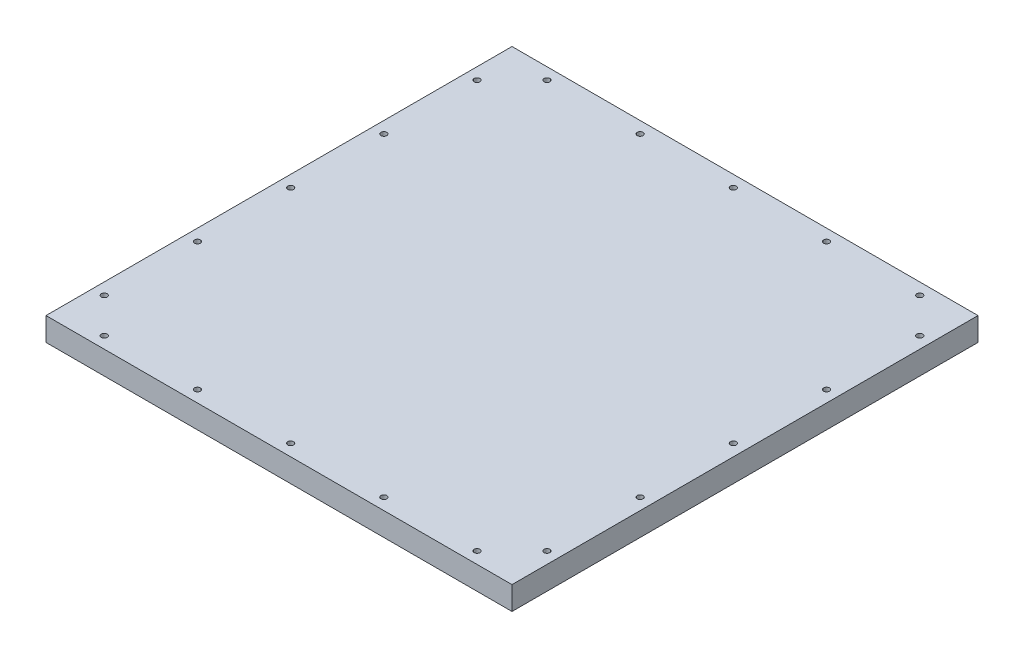
SolidWorks part; units mm, degrees
ref_plane "Front Plane" through (0, 0, 0) normal (0, 0, 1) x (1, 0, 0)
ref_plane "Top Plane" through (0, 0, 0) normal (0, 1, 0) x (1, 0, 0)
ref_plane "Right Plane" through (0, 0, 0) normal (1, 0, 0) x (0, 0, -1)
sketch "Sketch1" plane through (0, 0, 0) normal (0, 1, 0) x (1, 0, 0)
  line L1 (0, 0) -> (254, 0)
  line L2 (0, 0) -> (0, 254)
  line L3 (0, 254) -> (254, 254)
  line L4 (254, 0) -> (254, 254)
  circle A0 centre (6.35, 25.4) radius 1.5875
  circle A1 centre (247.65, 25.4) radius 1.5875
  circle A2 centre (6.35, 76.2) radius 1.5875
  circle A3 centre (247.65, 76.2) radius 1.5875
  circle A4 centre (6.35, 127) radius 1.5875
  circle A5 centre (247.65, 127) radius 1.5875
  circle A6 centre (6.35, 177.8) radius 1.5875
  circle A7 centre (247.65, 177.8) radius 1.5875
  circle A8 centre (6.35, 228.6) radius 1.5875
  circle A9 centre (247.65, 228.6) radius 1.5875
  circle A10 centre (25.4, 6.35) radius 1.5875
  circle A11 centre (76.2, 6.35) radius 1.5875
  circle A12 centre (127, 6.35) radius 1.5875
  circle A13 centre (177.8, 6.35) radius 1.5875
  circle A14 centre (228.6, 6.35) radius 1.5875
  circle A15 centre (25.4, 247.65) radius 1.5875
  circle A16 centre (76.2, 247.65) radius 1.5875
  circle A17 centre (127, 247.65) radius 1.5875
  circle A18 centre (177.8, 247.65) radius 1.5875
  circle A19 centre (228.6, 247.65) radius 1.5875
  dimension "D1" = 2
  dimension "D2" = 5
  dimension "D3" = 5
  dimension "D4" = 2
extrude "Boss-Extrude1" add sketch "Sketch1" along normal blind 12.7
